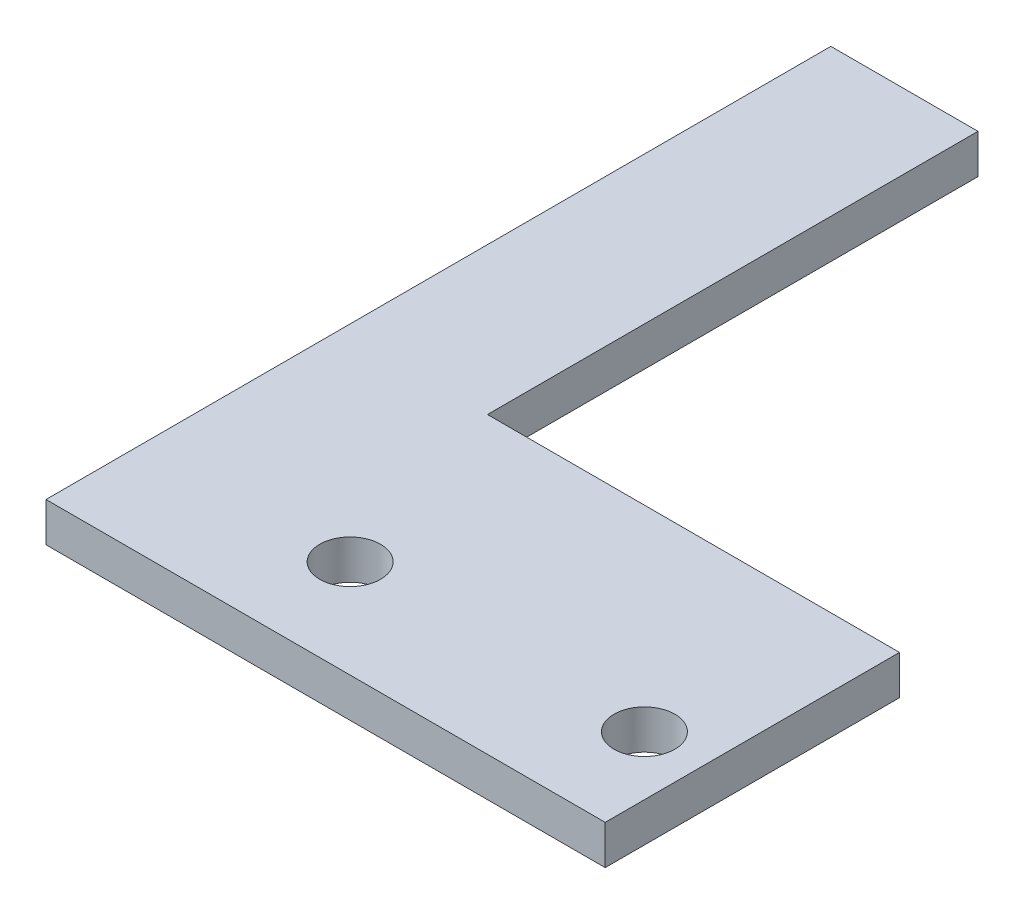
SolidWorks part; units mm, degrees
material "6061-T6 (SS)"
ref_plane "Front Plane" through (0, 0, 0) normal (0, 0, 1) x (1, 0, 0)
ref_plane "Top Plane" through (0, 0, 0) normal (0, 1, 0) x (1, 0, 0)
ref_plane "Right Plane" through (0, 0, 0) normal (1, 0, 0) x (0, 0, -1)
sketch "Sketch1" plane through (0, 0, 0) normal (0, 1, 0) x (1, 0, 0)
  line L0 (0, 0) -> (0, 40)
  line L1 (0, 40) -> (7.5, 40)
  line L2 (7.5, 40) -> (7.5, 15)
  line L3 (7.5, 15) -> (28.5, 15)
  line L4 (28.5, 15) -> (28.5, 0)
  line L5 (28.5, 0) -> (0, 0)
  dimension "D1" = 40
  dimension "D2" = 21
  dimension "D3" = 7.5
  dimension "D4" = 25
extrude "Boss-Extrude1" add sketch "Sketch1" along normal blind 2
hole_wizard "Ø3.1 (3.1) Diameter Hole1" positions "Sketch2" profile "Sketch3" hole size "Ø3.1" standard "ANSI Metric"
sketch "Sketch2" plane through (0, 2, 0) normal (0, 1, 0) x (1, 0, 0)
  line L2 (0, 0) -> (28.5, 0) construction
  line L3 (28.5, 0) -> (28.5, 15) construction
  point P6 (10.5, 5)
  point P8 (25.5, 5)
  dimension "D1" = 3
  dimension "D4" = 15
  dimension "D6" = 5
sketch "Sketch3" plane through (10.5, 2, -5) normal (1, 0, 0) x (0, 0, 1)
  line L0 (0, 0) -> (0, 10.9313)
  line L1 (0, 10.9313) -> (1.55, 10)
  line L2 (1.55, 10) -> (1.55, 0)
  line L5 (1.55, 0) -> (0, 0)
  line L10 (0, 10.9313) -> (-1.55, 10) construction
  line L11 (0, -6.35) -> (0, 107.95) construction
  dimension "Hole Dia." = 3.1
  dimension "Hole Depth" = 10
  dimension "Drill Angle" = 118
